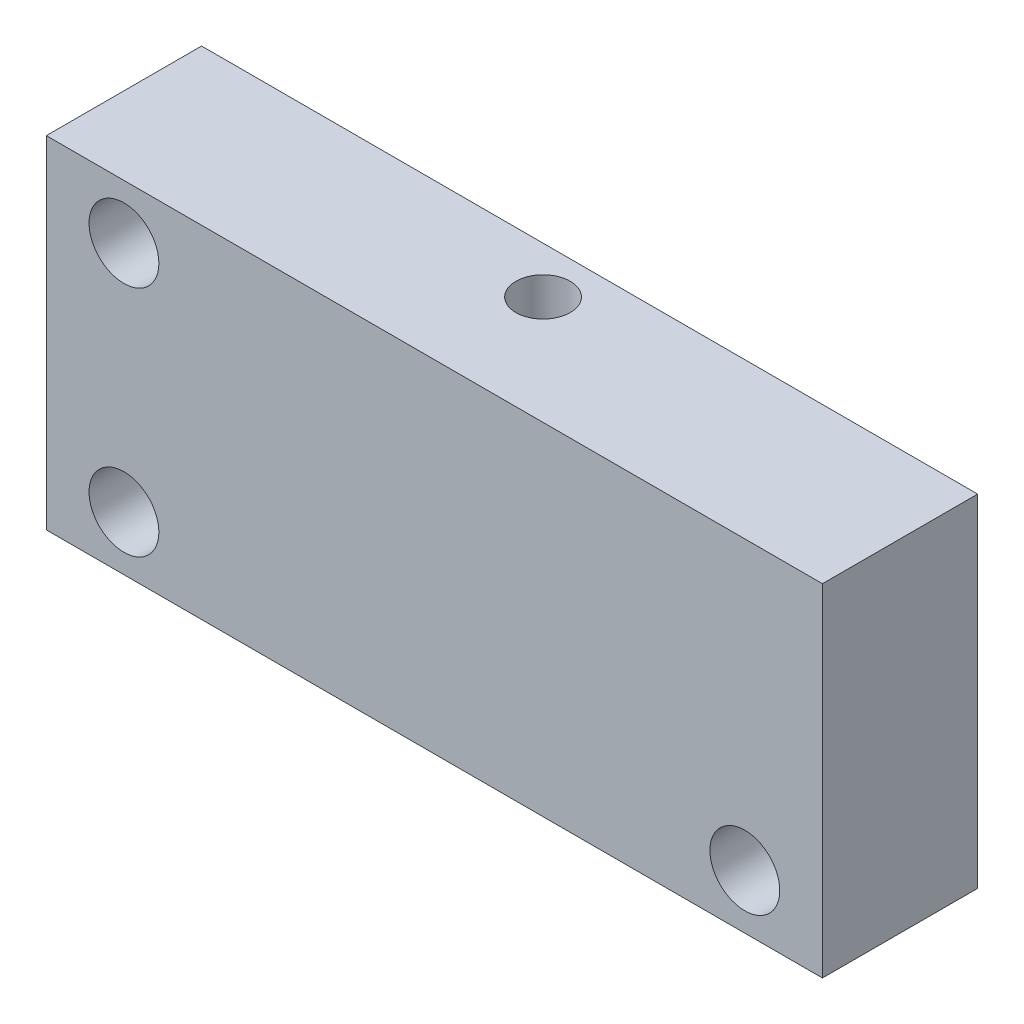
SolidWorks part; units mm, degrees
material "ABS PC"
ref_plane "Ebene vorne" through (0, 0, 0) normal (0, 0, 1) x (1, 0, 0)
ref_plane "Ebene oben" through (0, 0, 0) normal (0, 1, 0) x (1, 0, 0)
ref_plane "Ebene rechts" through (0, 0, 0) normal (1, 0, 0) x (0, 0, -1)
sketch "Skizze1" plane through (0, 0, 0) normal (0, 0, 1) x (1, 0, 0)
  line L1 (25, -11) -> (-25, -11)
  line L2 (25, -11) -> (25, 11)
  line L3 (25, 11) -> (-25, 11)
  line L4 (-25, -11) -> (-25, 11)
  line L5 (25, -11) -> (-25, 11) construction
  line L6 (25, 11) -> (-25, -11) construction
  point P0 (0, 0)
  dimension "D1" = 22
  dimension "D2" = 50
extrude "Aufsatz-Linear austragen1" add sketch "Skizze1" along normal blind 10
sketch "Skizze2" plane through (0, 0, 10) normal (0, 0, 1) x (1, 0, 0)
  line L0 (-20, 7.5) -> (-20, -7.5) construction
  line L1 (-20, -7.5) -> (20, -7.5) construction
  circle A0 centre (-20, 7.5) radius 2.25
  circle A1 centre (-20, -7.5) radius 2.25
  circle A2 centre (20, -7.5) radius 2.25
  point P6 (-20, 0)
  point P7 (0, -7.5)
  dimension "D3" = 4.5
  dimension "D1" = 15
  dimension "D2" = 40
extrude "Schnitt-Linear austragen1" cut sketch "Skizze2" against normal through all
sketch "Skizze3" plane through (0, 0, 0) normal (0, 0, -1) x (-1, 0, 0)
  line L1 (6.45, -6.45) -> (-6.45, -6.45)
  line L2 (6.45, -6.45) -> (6.45, 6.45)
  line L3 (6.45, 6.45) -> (-6.45, 6.45)
  line L4 (-6.45, -6.45) -> (-6.45, 6.45)
  line L5 (6.45, -6.45) -> (-6.45, 6.45) construction
  line L6 (6.45, 6.45) -> (-6.45, -6.45) construction
  point P0 (0, 0)
  dimension "D1" = 12.9
extrude "Schnitt-Linear austragen2" cut sketch "Skizze3" against normal blind 6
sketch "Skizze4" plane through (0, 0, 0) normal (0, 0, -1) x (-1, 0, 0)
  circle A0 centre (-6.45, 6.45) radius 2
  circle A1 centre (6.45, 6.45) radius 2
  circle A2 centre (-6.45, -6.45) radius 2
  circle A3 centre (6.45, -6.45) radius 2
  dimension "D1" = 4
extrude "Schnitt-Linear austragen3" cut sketch "Skizze4" against normal blind 6.1
sketch "Skizze5" plane through (0, 11, 0) normal (0, 1, 0) x (1, 0, 0)
  circle A0 centre (0, -3) radius 1.75
  point P2 (0, 0)
  dimension "D2" = 3.5
  dimension "D1" = 3
extrude "Schnitt-Linear austragen4" cut sketch "Skizze5" against normal blind 6.1
